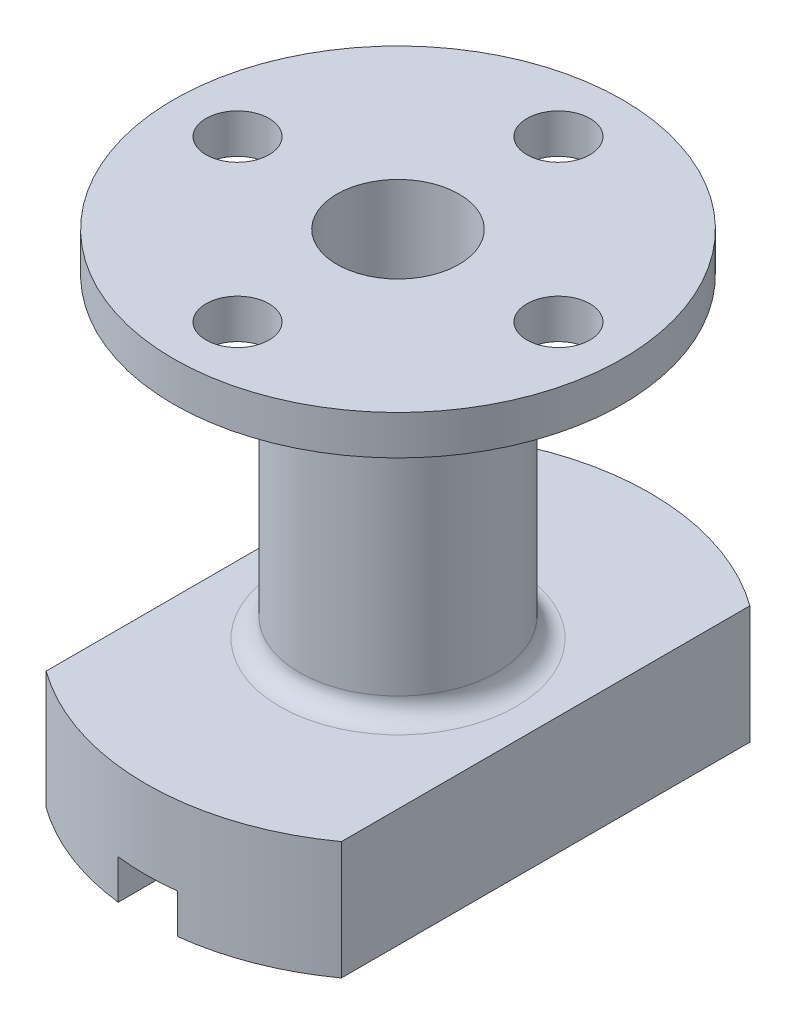
SolidWorks part; units mm, degrees
ref_plane "前视基准面" through (0, 0, 0) normal (0, 0, 1) x (1, 0, 0)
ref_plane "上视基准面" through (0, 0, 0) normal (0, 1, 0) x (1, 0, 0)
ref_plane "右视基准面" through (0, 0, 0) normal (1, 0, 0) x (0, 0, -1)
sketch "草图1" plane through (0, 0, 0) normal (0, 1, 0) x (1, 0, 0)
  line L0 (-7.5, 10.3726) -> (-7.5, -10.3726)
  line L1 (0, -1000) -> (0, 49000) construction
  line L2 (7.5, 10.3726) -> (7.5, -10.3726)
  arc A0 (-7.5, -10.3726) -> (7.5, -10.3726) centre (0, 0) ccw
  arc A1 (7.5, 10.3726) -> (-7.5, 10.3726) centre (0, 0) ccw
  dimension "D1" = 25.6
  dimension "D2" = 7.5
extrude "凸台-拉伸1" add sketch "草图1" along normal blind 6
sketch "草图2" plane through (0, 0, 0) normal (0, -1, 0) x (1, 0, 0)
  line L0 (-1.5, 12.7118) -> (-1.5, -12.7118)
  line L1 (0, -1000) -> (0, 49000) construction
  line L2 (1.5, 12.7118) -> (1.5, -12.7118)
  line L5 (7.5, -10.3726) -> (7.5, 10.3726)
  line L6 (-7.5, 10.3726) -> (-7.5, -10.3726)
  arc A0 (7.5, 10.3726) -> (-7.5, 10.3726) centre (0, 0) ccw construction
  arc A1 (-7.5, -10.3726) -> (7.5, -10.3726) centre (0, 0) ccw construction
  arc A4 (-7.5, -10.3726) -> (7.5, -10.3726) centre (0, 0) ccw
  arc A5 (7.5, 10.3726) -> (-7.5, 10.3726) centre (0, 0) ccw
  arc A6 (-1.5, -12.7118) -> (1.5, -12.7118) centre (0, 0) ccw
  arc A7 (1.5, 12.7118) -> (-1.5, 12.7118) centre (0, 0) ccw
  dimension "D1" = 1.5
  dimension "D2" = 0
extrude "切除-拉伸1" cut sketch "草图2" against normal blind 2
sketch "草图4" plane through (0, 6, 0) normal (0, 1, 0) x (1, 0, 0)
  circle A0 centre (0, 0) radius 5
  dimension "D1" = 10
extrude "凸台-拉伸2" add sketch "草图4" along normal blind 16
sketch "草图7" plane through (0, 0, 0) normal (0, -1, 0) x (1, 0, 0)
  circle A0 centre (0, 0) radius 3.1
  dimension "D1" = 6.2
extrude "切除-拉伸3" cut sketch "草图7" against normal up to next
fillet "圆角1" radius 1 1 edges at (0, 6, 5)
sketch "草图8" plane through (0, 22, 0) normal (0, 1, 0) x (1, 0, 0)
  circle A0 centre (0, 0) radius 11.4
  dimension "D1" = 22.8
extrude "凸台-拉伸3" add sketch "草图8" along normal blind 2
sketch "草图9" plane through (0, 22, 0) normal (0, -1, 0) x (1, 0, 0)
  circle A1 centre (0, 0) radius 3.1
  circle A2 centre (0, 0) radius 3.1
  dimension "D1" = 0
extrude "切除-拉伸4" cut sketch "草图9" against normal blind 2
sketch "草图10" plane through (0, 24, 0) normal (0, 1, 0) x (1, 0, 0)
  line L0 (-1000, 0) -> (49000, 0) construction
  line L1 (-707.1068, -707.1068) -> (34648.2323, 34648.2323) construction
  circle A0 centre (0, 8.15) radius 1.6
  circle A1 centre (0, -8.15) radius 1.6
  circle A2 centre (-8.15, 0) radius 1.6
  circle A3 centre (8.15, 0) radius 1.6
  dimension "D1" = 3.2
  dimension "D2" = 16.3
  dimension "D3" = 45
extrude "切除-拉伸5" cut sketch "草图10" against normal blind 2
